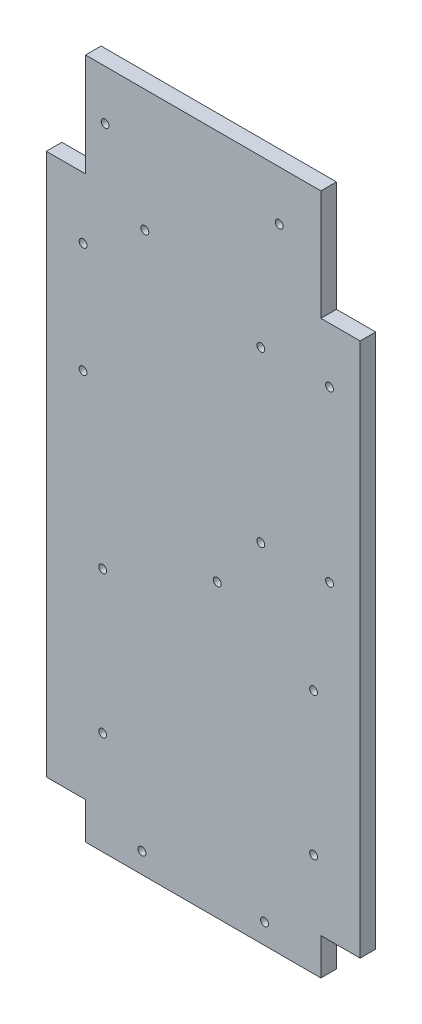
SolidWorks part; units mm, degrees
ref_plane "Front Plane" through (0, 0, 0) normal (0, 0, 1) x (1, 0, 0)
ref_plane "Top Plane" through (0, 0, 0) normal (0, 1, 0) x (1, 0, 0)
ref_plane "Right Plane" through (0, 0, 0) normal (1, 0, 0) x (0, 0, -1)
sketch "Sketch1" plane through (0, 0, 0) normal (0, 0, 1) x (1, 0, 0)
  line L1 (0, 0) -> (128, 0)
  line L2 (0, 0) -> (0, 278)
  line L3 (0, 278) -> (128, 278)
  line L4 (128, 0) -> (128, 278)
  dimension "D1" = 278
  dimension "D2" = 128
extrude "Boss-Extrude1" add sketch "Sketch1" along normal blind 6.35
sketch "Sketch2" plane through (0, 0, 6.35) normal (0, 0, 1) x (1, 0, 0)
  line L1 (0, 278) -> (16, 278)
  line L2 (0, 278) -> (0, 236)
  line L3 (0, 236) -> (16, 236)
  line L4 (16, 278) -> (16, 236)
  line L5 (128, 278) -> (112, 278)
  line L6 (128, 278) -> (128, 233)
  line L7 (128, 233) -> (112, 233)
  line L8 (112, 278) -> (112, 233)
  line L9 (128, 0) -> (112, 0)
  line L10 (128, 0) -> (128, 15)
  line L11 (128, 15) -> (112, 15)
  line L12 (112, 0) -> (112, 15)
  line L13 (0, 0) -> (16, 0)
  line L14 (0, 0) -> (0, 15)
  line L15 (0, 15) -> (16, 15)
  line L16 (16, 0) -> (16, 15)
  dimension "D1" = 16
  dimension "D2" = 16
  dimension "D3" = 16
  dimension "D4" = 16
  dimension "D5" = 15
  dimension "D6" = 15
  dimension "D7" = 45
  dimension "D8" = 42
extrude "Cut-Extrude1" cut sketch "Sketch2" against normal blind 31.7625
sketch "Sketch5" plane through (0, 0, 6.35) normal (0, 0, 1) x (1, 0, 0)
  circle A0 centre (24, 257.75) radius 1.6
  circle A1 centre (95, 257.75) radius 1.6
  circle A2 centre (87.5, 210.5) radius 1.6
  circle A3 centre (115.5, 210.5) radius 1.6
  circle A4 centre (87.5, 141.5) radius 1.6
  circle A5 centre (115.5, 141.5) radius 1.6
  circle A6 centre (69.6974, 118.75) radius 1.6
  circle A7 centre (40.1974, 228.25) radius 1.6
  circle A8 centre (15, 211) radius 1.6
  circle A9 centre (15, 166) radius 1.6
  circle A10 centre (39, 8.3089) radius 1.6
  circle A11 centre (89, 8.3089) radius 1.6
  circle A12 centre (23, 100) radius 1.6
  circle A13 centre (23, 42) radius 1.6
  circle A14 centre (109, 42) radius 1.6
  circle A15 centre (109, 100) radius 1.6
  dimension "D1" = 3.2
  dimension "D2" = 3.2
  dimension "D3" = 3.2
  dimension "D4" = 3.2
  dimension "D5" = 3.2
  dimension "D6" = 3.2
  dimension "D7" = 3.2
  dimension "D8" = 3.2
  dimension "D9" = 3.2
  dimension "D10" = 3.2
  dimension "D11" = 3.2
  dimension "D12" = 3.2
  dimension "D13" = 3.2
  dimension "D14" = 3.2
  dimension "D15" = 3.2
  dimension "D16" = 3.2
extrude "Cut-Extrude3" cut sketch "Sketch5" against normal blind 10
